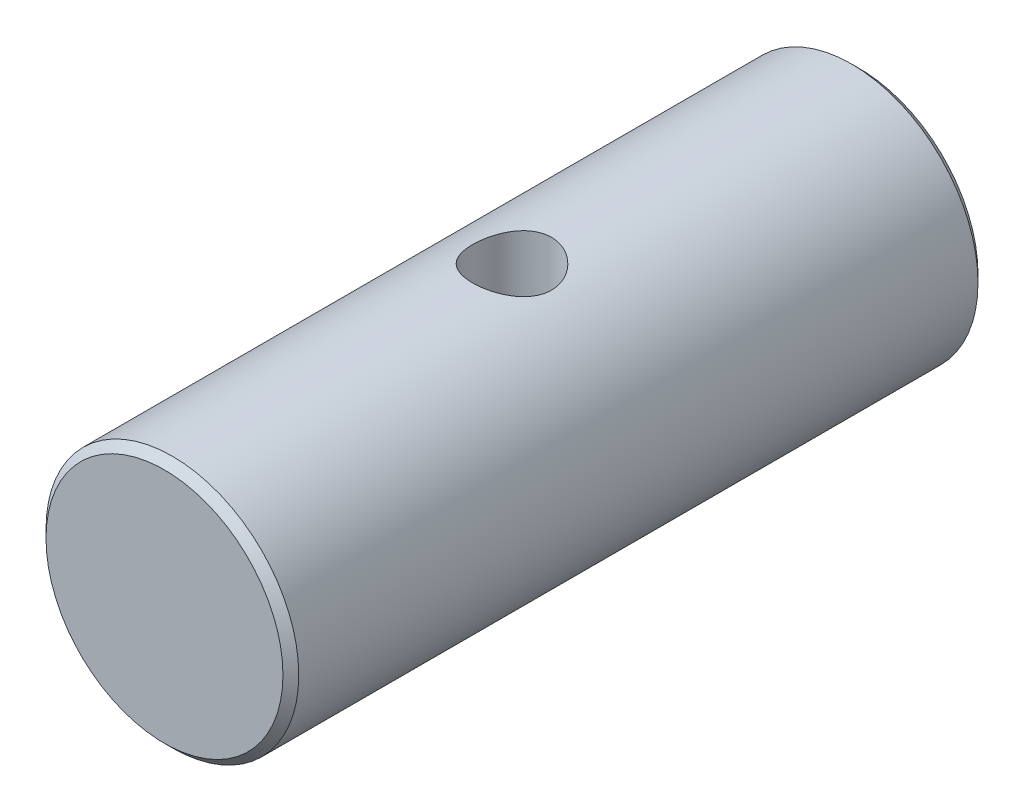
SolidWorks part; units mm, degrees
ref_plane "Front Plane" through (0, 0, 0) normal (0, 0, 1) x (1, 0, 0)
ref_plane "Top Plane" through (0, 0, 0) normal (0, 1, 0) x (1, 0, 0)
ref_plane "Right Plane" through (0, 0, 0) normal (1, 0, 0) x (0, 0, -1)
sketch "Sketch1" plane through (0, 0, 0) normal (0, 0, 1) x (1, 0, 0)
  circle A0 centre (0, 0) radius 8
  dimension "D1" = 16
extrude "Boss-Extrude1" add sketch "Sketch1" along normal blind 44
sketch "Sketch2" plane through (0, 0, 0) normal (0, 1, 0) x (1, 0, 0)
  line L0 (8, -44) -> (8, 0) construction
  circle A0 centre (0, -22) radius 2.5
  dimension "D3" = 5
  dimension "D1" = 22
  dimension "D2" = 8
extrude "Cut-Extrude1" cut sketch "Sketch2" against normal through all both and the other way through all
chamfer "Chamfer1" distance 0.5 2 edges at (8, 0, 0) (8, 0, 44)
